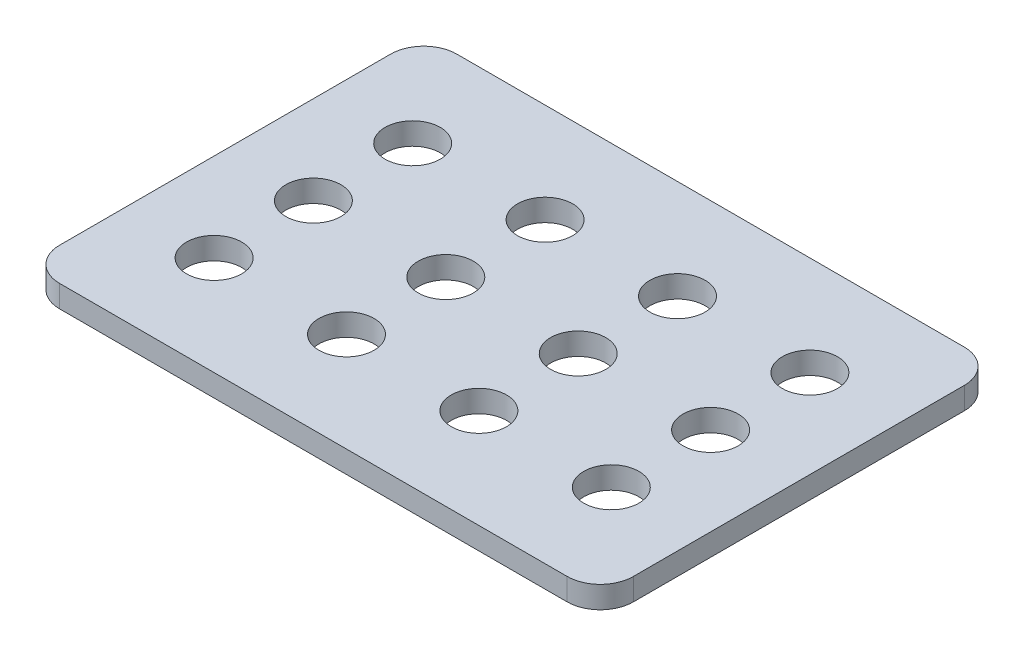
SolidWorks part; units mm, degrees
ref_plane "Front Plane" through (0, 0, 0) normal (0, 0, 1) x (1, 0, 0)
ref_plane "Top Plane" through (0, 0, 0) normal (0, 1, 0) x (1, 0, 0)
ref_plane "Right Plane" through (0, 0, 0) normal (1, 0, 0) x (0, 0, -1)
sketch "Sketch1" plane through (0, 0, 0) normal (0, 1, 0) x (1, 0, 0)
  line L1 (-115, -90) -> (115, -90)
  line L2 (-130, -75) -> (-130, 75)
  line L3 (-115, 90) -> (115, 90)
  line L4 (130, -75) -> (130, 75)
  line L5 (-130, -90) -> (130, 90) construction
  line L6 (-130, 90) -> (130, -90) construction
  circle A0 centre (-90, 45) radius 12.5
  circle A1 centre (-30, 45) radius 12.5
  circle A2 centre (30, 45) radius 12.5
  circle A3 centre (90, 45) radius 12.5
  circle A4 centre (-30, 0) radius 12.5
  circle A5 centre (30, 0) radius 12.5
  circle A6 centre (90, 0) radius 12.5
  circle A7 centre (-30, -45) radius 12.5
  circle A8 centre (30, -45) radius 12.5
  circle A9 centre (90, -45) radius 12.5
  circle A10 centre (-90, 0) radius 12.5
  circle A11 centre (-90, -45) radius 12.5
  arc A12 (-115, -90) -> (-130, -75) centre (-115, -75) cw
  arc A13 (115, -90) -> (130, -75) centre (115, -75) ccw
  arc A14 (115, 90) -> (130, 75) centre (115, 75) cw
  arc A15 (-130, 75) -> (-115, 90) centre (-115, 75) cw
  point P0 (0, 0)
  point P9 (0, 0)
  dimension "D4" = 45
  dimension "D3" = 40
  dimension "D5" = 25
  dimension "D8" = 15
  dimension "D1" = 260
  dimension "D2" = 180
  dimension "D6" = 4
  dimension "D7" = 3
extrude "Boss-Extrude1" add sketch "Sketch1" along normal mid plane 10
